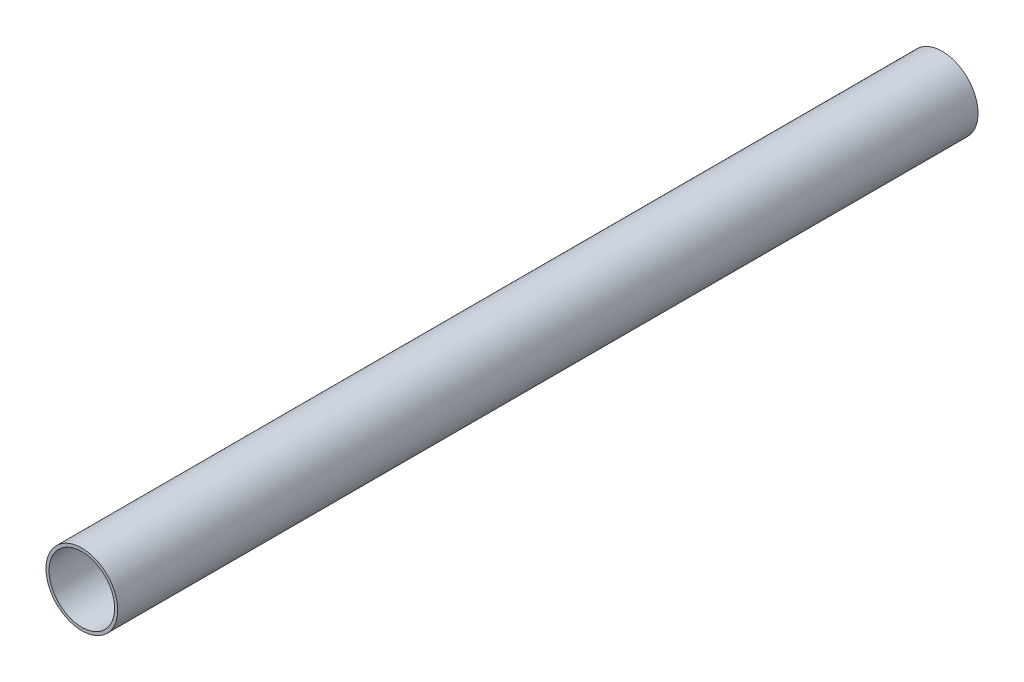
SolidWorks part; units mm, degrees
material "Hexcel AS4C (3000 丝)"
ref_plane "前视基准面" through (0, 0, 0) normal (0, 0, 1) x (1, 0, 0)
ref_plane "上视基准面" through (0, 0, 0) normal (0, 1, 0) x (1, 0, 0)
ref_plane "右视基准面" through (0, 0, 0) normal (1, 0, 0) x (0, 0, -1)
ref_plane "基准面4" through (0, 70.7107, 0) normal (0, -1, 0) x (1, 0, 0)
sketch "草图1" plane through (0, 70.7107, 0) normal (0, -1, 0) x (1, 0, 0)
  line L0 (-60.2967, 211.9) -> (-61.1857, 211.9)
  line L1 (-61.1857, 211.9) -> (-61.1857, -38.1)
  line L2 (-61.1857, -38.1) -> (-60.2967, -38.1)
  line L3 (-60.2967, -38.1) -> (-60.2967, 211.9)
  line L4 (-70.7107, 387.35) -> (-70.7107, -38.1) construction
revolve "旋转1" add sketch "草图1" angle 360 about L4
